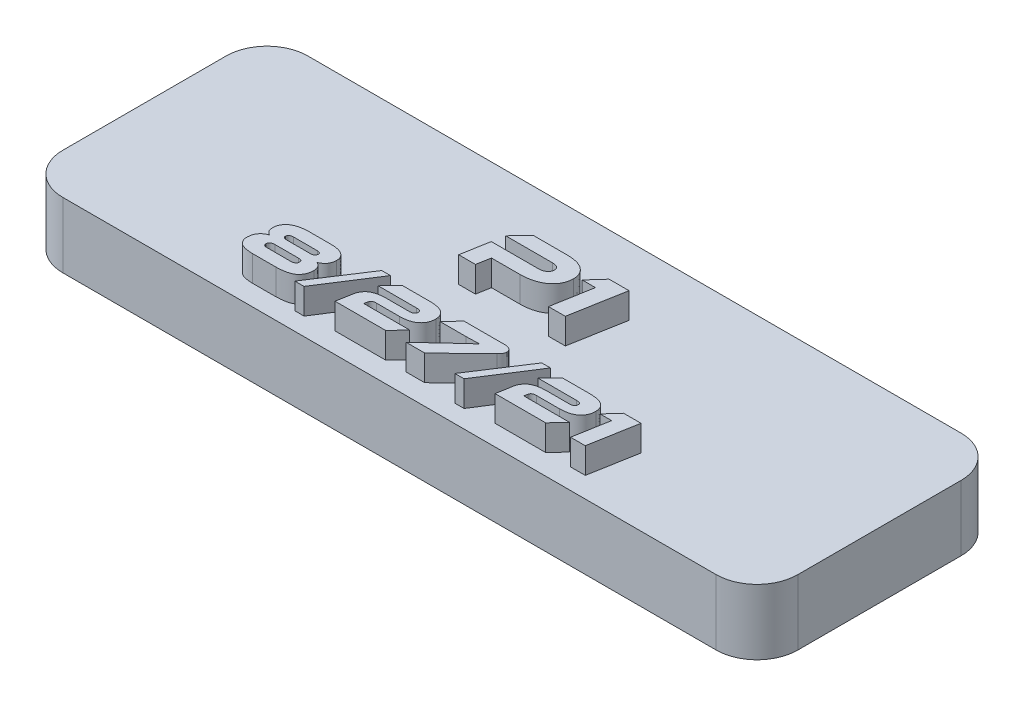
SolidWorks part; units mm, degrees
ref_plane "Front Plane" through (0, 0, 0) normal (0, 0, 1) x (1, 0, 0)
ref_plane "Top Plane" through (0, 0, 0) normal (0, 1, 0) x (1, 0, 0)
ref_plane "Right Plane" through (0, 0, 0) normal (1, 0, 0) x (0, 0, -1)
sketch "Sketch1" plane through (0, 0, 0) normal (0, 1, 0) x (1, 0, 0)
  line L1 (-28.575, 9.525) -> (28.575, 9.525)
  line L2 (-28.575, 9.525) -> (-28.575, -9.525)
  line L3 (-28.575, -9.525) -> (28.575, -9.525)
  line L4 (28.575, 9.525) -> (28.575, -9.525)
  line L5 (-28.575, 9.525) -> (28.575, -9.525) construction
  line L6 (-28.575, -9.525) -> (28.575, 9.525) construction
  point P0 (0, 0)
  dimension "D1" = 57.15
  dimension "D2" = 19.05
extrude "Boss-Extrude1" add sketch "Sketch1" along normal up to surface (5.08 mm away)
fillet "Fillet1" radius 3.175 4 edges at (-28.575, 2.54, 9.525) (-28.575, 2.54, -9.525) (28.575, 2.54, 9.525) (28.575, 2.54, -9.525)
sketch "Sketch3" plane through (0, 5.08, 0) normal (0, 1, 0) x (1, 0, 0)
  line L0 (28.575, -7.9375) -> (-28.575, -7.9375) construction
  line L1 (28.575, -6.35) -> (28.575, 6.35) construction
  line L2 (-28.575, 6.35) -> (-28.575, -6.35) construction
  line L3 (28.575, 0) -> (-28.575, 0) construction
  line L5 (-25.4, -9.525) -> (25.4, -9.525) construction
  line L6 (25.4, 9.525) -> (-25.4, 9.525) construction
  text T0 "P1" font "Ethnocentric Rg" height in points 16
  text T1 "8/27/21" font "Ethnocentric Rg" height in points 14
  point P8 (-28.575, 0)
  dimension "D1" = 1.5875
extrude "Boss-Extrude2" add sketch "Sketch3" along normal blind 2
sketch "Sketch4" plane through (0, 0, 0) normal (0, -1, 0) x (1, 0, 0)
  line L0 (25.4, 0) -> (-25.4, 0) construction
  circle A0 centre (-25.4, 0) radius 0.9
  circle A1 centre (25.4, 0) radius 0.9
  point P3 (0, 0)
  dimension "D2" = 1.8
  dimension "D1" = 50.8
extrude "Cut-Extrude1" cut sketch "Sketch4" against normal blind 4
